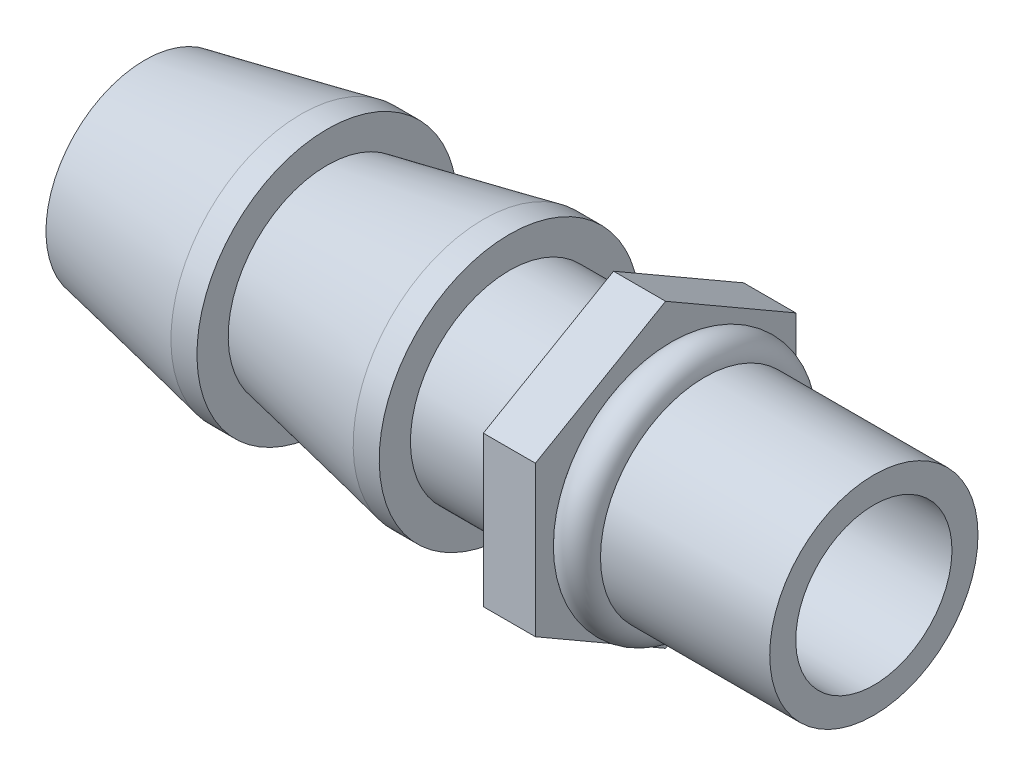
SolidWorks part; units mm, degrees
ref_plane "Plan de face" through (0, 0, 0) normal (0, 0, 1) x (1, 0, 0)
ref_plane "Plan de dessus" through (0, 0, 0) normal (0, 1, 0) x (1, 0, 0)
ref_plane "Plan de droite" through (0, 0, 0) normal (1, 0, 0) x (0, 0, -1)
sketch "Esquisse1" plane through (0, 0, 0) normal (0, 0, 1) x (1, 0, 0)
  line L0 (0, 0) -> (-10.75, 0) construction
  line L1 (-10.75, 1.5) -> (-10.75, -1.5) construction
  line L2 (-7.25, 2.5) -> (-7.25, -2.5) construction
  line L3 (-10.75, 1.5) -> (-1.75, 1.5)
  line L4 (-10.75, 1.5) -> (-10.75, 1.9)
  line L5 (-10.75, 1.9) -> (-7.75, 2.5)
  line L6 (-7.25, 2.5) -> (-7.25, 1.9)
  line L7 (-7.25, 1.9) -> (-4.25, 2.5)
  line L8 (-7.75, 2.5) -> (-7.25, 2.5)
  line L9 (-10.75, 1.9) -> (-1.75, 1.9) construction
  line L10 (-7.25, 2.5) -> (-4.25, 2.5) construction
  line L11 (-4.25, 2.5) -> (-3.75, 2.5)
  line L12 (-3.75, 2.5) -> (-3.75, 1.9)
  line L13 (-3.75, 1.9) -> (-1.75, 1.9)
  line L14 (-1.75, 1.9) -> (-1.75, 1.5)
  line L15 (-10.75, 1.9) -> (-10.75, 2.5) construction
  line L16 (-10.75, 2.5) -> (-7.75, 2.5) construction
  line L17 (-0.75, 2) -> (-0.75, 0) construction
  circle A0 centre (-0.375, 2) radius 0.375
  point P6 (-10.75, 0)
  point P9 (-7.25, 0)
  dimension "D8" = 0.75
  dimension "D1" = 3
  dimension "D2" = 5
  dimension "D3" = 0.4
  dimension "D4" = 10.75
  dimension "D5" = 0.5
  dimension "D6" = 3.5
  dimension "D7" = 2
  dimension "D9" = 1
  dimension "D10" = 2
revolve "Révolution1" add sketch "Esquisse1" angle 360 about L0
sketch "Esquisse2" plane through (-1.75, 0, 0) normal (1, 0, 0) x (0, 0, -1)
  line L0 (-2.5, -1.4434) -> (-2.5, 1.4434)
  line L1 (-2.5, 1.4434) -> (0, 2.8868)
  line L2 (0, 2.8868) -> (2.5, 1.4434)
  line L3 (2.5, 1.4434) -> (2.5, -1.4434)
  line L4 (2.5, -1.4434) -> (0, -2.8868)
  line L5 (0, -2.8868) -> (-2.5, -1.4434)
  line L6 (-2.5, 1.4434) -> (2.5, 1.4434) construction
  line L7 (-2.5, 1.4434) -> (2.5, -1.4434) construction
  circle A0 centre (0, 0) radius 1.5
  point P4 (0, 0)
  dimension "D3" = 3
  dimension "D1" = 5
  dimension "D2" = 5
extrude "Boss.-Extru.1" add sketch "Esquisse2" along normal blind 1
sketch "Esquisse3" plane through (-0.75, 0, 0) normal (1, 0, 0) x (0, 0, -1)
  circle A0 centre (0, 0) radius 1.5
  circle A1 centre (0, 0) radius 2
  dimension "D1" = 3
  dimension "D2" = 4
extrude "Boss.-Extru.2" add sketch "Esquisse3" along normal blind 4
